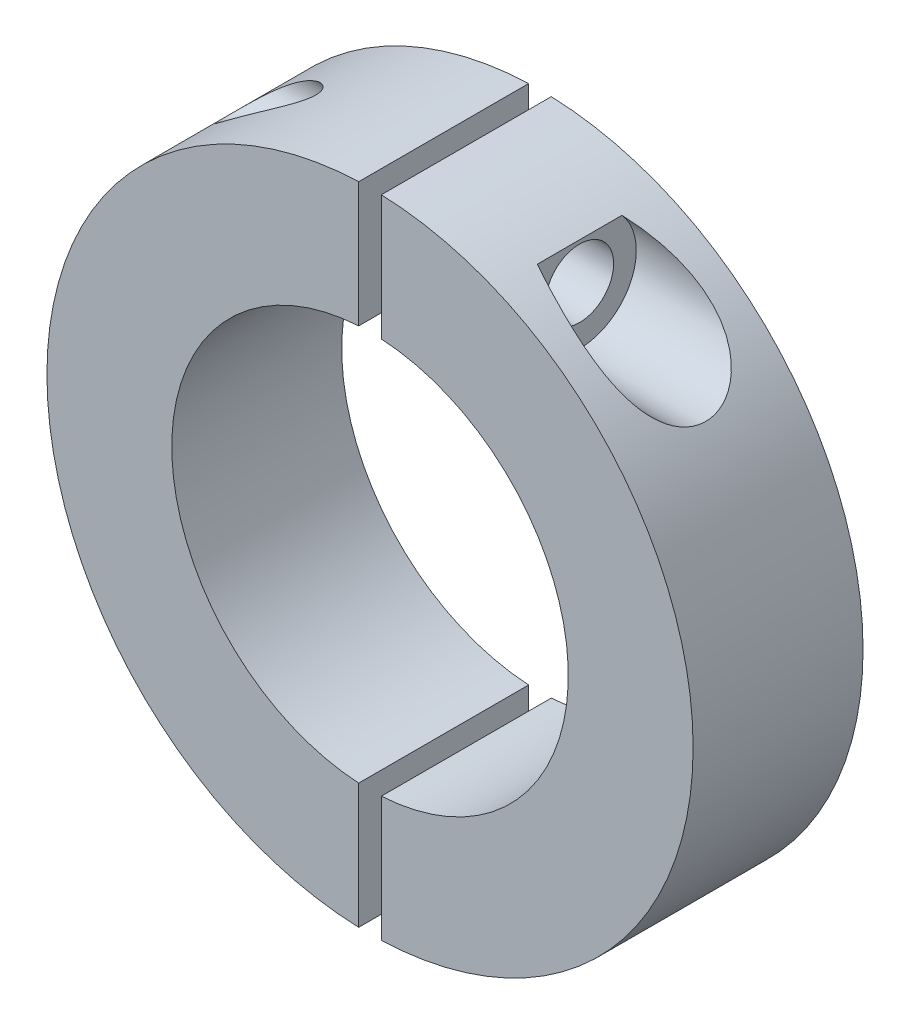
SolidWorks part; units mm, degrees
material "AISI 1020"
ref_plane "Спереди" through (0, 0, 0) normal (0, 0, 1) x (1, 0, 0)
ref_plane "Сверху" through (0, 0, 0) normal (0, 1, 0) x (1, 0, 0)
ref_plane "Справа" through (0, 0, 0) normal (1, 0, 0) x (0, 0, -1)
sketch "Эскиз1" plane through (0, 0, 0) normal (0, 0, 1) x (1, 0, 0)
  line L0 (0.2322, 23.5) -> (14, 23.5) construction
  line L1 (-1, 17.4714) -> (1, 17.4714) construction
  line L2 (-1, 17.4714) -> (-1, 28.5)
  line L3 (-1, 28.5) -> (1, 28.5) construction
  line L4 (1, 17.4714) -> (1, 28.5)
  line L5 (-1000, 0) -> (49000, 0) construction
  line L6 (11, 18.5) -> (17, 18.5) construction
  line L7 (11, 18.5) -> (11, 28.5) construction
  line L8 (11, 28.5) -> (17, 28.5) construction
  line L9 (17, 18.5) -> (17, 28.5) construction
  line L10 (11, 18.5) -> (17, 28.5) construction
  line L11 (11, 28.5) -> (17, 18.5) construction
  line L12 (-10.5357, 20.5) -> (11, 20.5) construction
  line L13 (-10.5357, 20.5) -> (-10.5357, 26.5) construction
  line L14 (-10.5357, 26.5) -> (11, 26.5) construction
  line L15 (11, 20.5) -> (11, 26.5) construction
  line L16 (-10.5357, 20.5) -> (11, 26.5) construction
  line L17 (-10.5357, 26.5) -> (11, 20.5) construction
  line L18 (1, -17.4714) -> (1, -28.5)
  line L19 (-1, -17.4714) -> (-1, -28.5)
  circle A0 centre (0, 0) radius 17.5 construction
  arc A1 (-1, 17.4714) -> (-17.5, 0) centre (0, 0) ccw
  arc A2 (-1, 28.5) -> (-28.5175, 0) centre (0, 0) ccw
  arc A3 (28.5175, 0) -> (1, 28.5) centre (0, 0) ccw
  arc A4 (17.5, 0) -> (1, 17.4714) centre (0, 0) ccw
  arc A5 (1, -17.4714) -> (17.5, 0) centre (0, 0) ccw
  arc A6 (1, -28.5) -> (28.5175, 0) centre (0, 0) ccw
  arc A7 (-17.5, 0) -> (-1, -17.4714) centre (0, 0) ccw
  arc A8 (-28.5175, 0) -> (-1, -28.5) centre (0, 0) ccw
  point P7 (0, 17.4714)
  point P30 (0, 0)
  point P33 (0, 0)
  dimension "D4" = 2
  dimension "D1" = 2
  dimension "D2" = 10
  dimension "D3" = 6
  dimension "D5" = 6
  dimension "D6" = 10
  dimension "6" = 6
  dimension "D7" = 2
extrude "Бобышка-Вытянуть1" add sketch "Эскиз1" against normal up to surface (15 mm away) contours A2 A8 L19 A7 A1 L2 | L18 A6 A3 L4 A4 A5
ref_plane "Плоскость1" through (0, 0, 0) normal (1, 0, 0) x (0, 0, -1)
sketch "Эскиз2" plane through (0, 0, 0) normal (1, 0, 0) x (0, 0, -1)
  line L1 (15, 28.5) -> (0, 28.5) construction
  line L2 (7.5, 22.9857) -> (0, 22.9857) construction
  line L4 (0, 17.4714) -> (0, 28.5) construction
  circle A0 centre (7.5, 22.9857) radius 2.75
  point P6 (7.5, 28.5)
  point P13 (0, 22.9857)
  dimension "D1" = 5.5
extrude "Вырез-Вытянуть1" cut sketch "Эскиз2" against normal through all both and the other way through all
cosmetic thread "Условное изображение резьбы1" parameters "D2"=6
ref_plane "Плоскость2" through (11, 0, 0) normal (1, 0, 0) x (0, 0, -1)
sketch "Эскиз3" plane through (11, 0, 0) normal (1, 0, 0) x (0, 0, -1)
  circle A0 centre (7.5, 22.9857) radius 5
  circle A1 centre (7.5, 22.9857) radius 2.75 construction
  dimension "D1" = 10
extrude "Вырез-Вытянуть2" cut sketch "Эскиз3" along normal through all
sketch "Эскиз4" plane through (11, 0, 0) normal (1, 0, 0) x (0, 0, -1)
  circle A0 centre (7.5, 22.9857) radius 3
  circle A1 centre (7.5, 22.9857) radius 2.75 construction
  dimension "D1" = 6
extrude "Вырез-Вытянуть3" cut sketch "Эскиз4" against normal up to surface (10 mm away) up to face at (1, 22.9857, -10.25)
ref_axis "Ось1" through (0, 0, -80.9) along (0, 0, 1)
pattern_circular "Круговой массив1" count 2 over 360 about axis through (0, 0, -80.9) along (0, 0, 1) of "Вырез-Вытянуть1", "Вырез-Вытянуть2", "Вырез-Вытянуть3"
